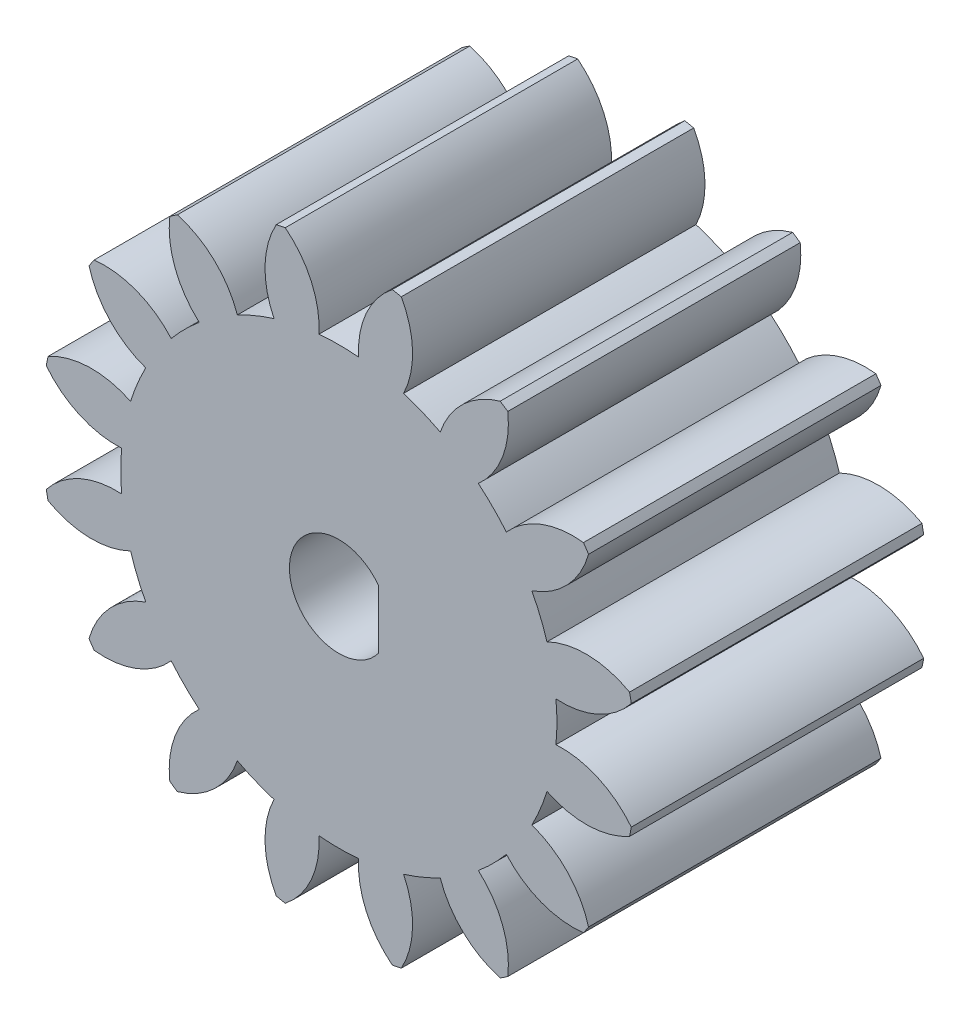
SolidWorks part; units mm, degrees
ref_plane "Front Plane" through (0, 0, 0) normal (0, 0, 1) x (1, 0, 0)
ref_plane "Top Plane" through (0, 0, 0) normal (0, 1, 0) x (1, 0, 0)
ref_plane "Right Plane" through (0, 0, 0) normal (1, 0, 0) x (0, 0, -1)
sketch "Sketch1" plane through (0, 0, 0) normal (0, 0, 1) x (1, 0, 0)
  circle A0 centre (0, 0) radius 15
  dimension "D1" = 30
extrude "Boss-Extrude1" add sketch "Sketch1" along normal blind 14.75
sketch "Sketch2" plane through (0, 0, 14.75) normal (0, 0, 1) x (1, 0, 0)
  arc A0 (-1, 10.9545) -> (1, 10.9545) centre (0, 0) cw
  arc A1 (-2.7, 14.755) -> (2.7, 14.755) centre (0, 0) cw
  circle A2 centre (0, 0) radius 15 construction
  arc A3 (-2.7, 14.755) -> (-1, 10.9545) centre (-5.4918, 11.2257) cw
  arc A4 (1, 10.9545) -> (2.7, 14.755) centre (5.4918, 11.2257) cw
  point P10 (0, 11)
  point P11 (0, 15)
  dimension "D1" = 11
  dimension "D2" = 4.5
  dimension "D3" = 5.4
  dimension "D4" = 2
extrude "Cut-Extrude1" cut sketch "Sketch2" against normal through all
pattern_circular "CirPattern1" count 16 over 360 about axis through (0, 0, 0) along (0, 0, 1) of "Cut-Extrude1"
sketch "Sketch3" plane through (0, 0, 14.75) normal (0, 0, 1) x (1, 0, 0)
  line L0 (2.0058, 1.4754) -> (2.0058, -1.4754)
  arc A0 (2.0058, 1.4754) -> (2.0058, -1.4754) centre (0, 0) ccw
  point P3 (-2.49, 0)
  point P10 (2.0058, 0)
  dimension "D1" = 2.49
  dimension "D2" = 4.4958
extrude "Cut-Extrude2" cut sketch "Sketch3" against normal through all
